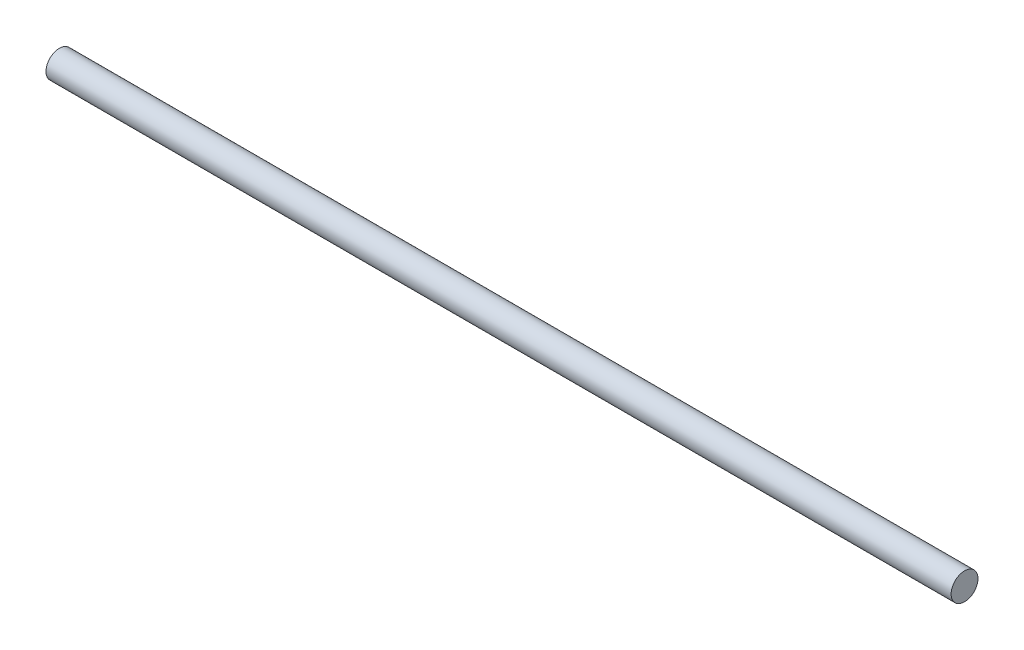
SolidWorks part; units mm, degrees
ref_plane "Front Plane" through (0, 0, 0) normal (0, 0, 1) x (1, 0, 0)
ref_plane "Top Plane" through (0, 0, 0) normal (0, 1, 0) x (1, 0, 0)
ref_plane "Right Plane" through (0, 0, 0) normal (1, 0, 0) x (0, 0, -1)
sketch "Sketch1" plane through (0, 0, 0) normal (1, 0, 0) x (0, 0, -1)
  circle A0 centre (0, 0) radius 2.375
  dimension "D1" = 4.75
extrude "Boss-Extrude1" add sketch "Sketch1" along normal blind 160
